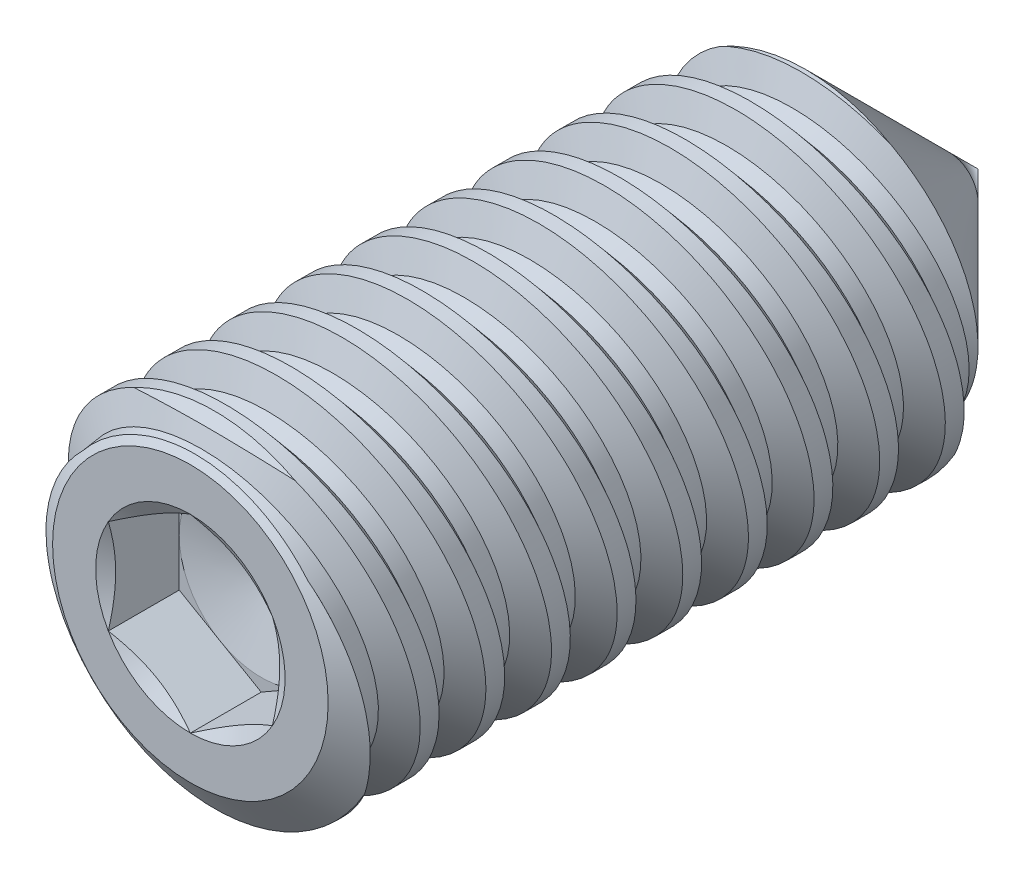
SolidWorks part; units mm, degrees
ref_plane "Front" through (0, 0, 0) normal (0, 0, 1) x (1, 0, 0)
ref_plane "Top" through (0, 0, 0) normal (0, 1, 0) x (1, 0, 0)
ref_plane "Right" through (0, 0, 0) normal (1, 0, 0) x (0, 0, -1)
sketch "Sketch22" plane through (0, 0, 0) normal (1, 0, 0) x (0, 0, -1)
  line L0 (-4.7625, 0) -> (-4.7625, 1.6662)
  line L1 (-4.7625, 1.6662) -> (-4.4708, 2.0828)
  line L2 (-4.4708, 2.0828) -> (2.6797, 2.0828)
  line L3 (2.6797, 2.0828) -> (4.7625, 2.0828) construction
  line L4 (2.6797, 2.0828) -> (4.7625, 0)
  line L5 (4.7625, 0) -> (-4.7625, 0)
  line L6 (5.271, 0) -> (4.7625, 0) construction
  line L7 (4.7625, 0) -> (4.7625, 2.0828) construction
  line L8 (2.6797, -2.0828) -> (4.7625, 0) construction
  line L10 (4.7625, -2.0828) -> (-4.7625, -2.0828) construction
  line L11 (-4.7625, -2.0828) -> (-4.7625, 0) construction
  line L12 (0, -2.0828) -> (0, 0) construction
  dimension "D1" = 7.4422
  dimension "Screw Dia" = 4.1656
  dimension "Length" = 9.525
  dimension "D3" = 35
  dimension "D7" = 3.3325
  dimension "Cone Point" = 90
revolve "Revolve1" add sketch "Sketch22" angle 360 about L6
sketch "Sketch6" plane through (0, 0, 0) normal (1, 0, 0) x (0, 0, -1)
  line L0 (1.9, 2.0828) -> (2.6937, -2.0828) construction
  line L1 (-4.4708, 2.0828) -> (2.6797, 2.0828) construction
  line L2 (2.6797, 2.0828) -> (2.6797, 2.2314) construction
  line L3 (1.9, 2.0828) -> (1.9974, 2.1014) construction
  line L4 (2.5165, 1.7629) -> (2.3215, 1.7258)
  line L5 (2.3215, 1.7258) -> (1.9974, 2.1014)
  line L6 (2.5165, 1.7629) -> (2.6797, 2.2314)
  line L7 (2.6797, 2.2314) -> (1.9974, 2.1014)
  line L8 (2.3545, 2.0828) -> (3.1482, -2.0828) construction
  line L9 (3.6028, 0.1622) -> (1.9, -0.1622) construction
  line L10 (2.3386, 2.1664) -> (2.419, 1.7443) construction
  line L12 (4.7625, -2.0828) -> (-4.7625, -2.0828) construction
  line L13 (1.9, -2.0828) -> (1.9, 2.0828) construction
  line L14 (1.9, -2.0828) -> (2.6937, -2.0828) construction
  line L15 (2.6937, -2.0828) -> (3.1482, -2.0828) construction
  line L18 (1.9, 2.0828) -> (2.3545, 2.0828) construction
  point P18 (2.7514, 0)
  dimension "D1" = 0.7937
  dimension "D2" = 0.1984
  dimension "D3" = 60
  dimension "D4" = 0.0992
  dimension "Pitch" = 0.7937
revolve "Cut-Revolve8" cut sketch "Sketch6" angle 360 about L9
pattern_linear "LPattern1" count 10 spacing 0.7937 along (0, 0, 1) count 2 spacing 0.7937 along (0, 0, 1) of "Cut-Revolve8"
sketch "Sketch23" plane through (0, 0, 4.7625) normal (0, 0, 1) x (1, 0, 0)
  line L1 (0, 1.1457) -> (-0.9922, 0.5728)
  line L2 (-0.9922, 0.5728) -> (-0.9922, -0.5728)
  line L3 (-0.9922, -0.5728) -> (0, -1.1457)
  line L4 (0, -1.1457) -> (0.9922, -0.5728)
  line L5 (0.9922, -0.5728) -> (0.9922, 0.5728)
  line L6 (0.9922, 0.5728) -> (0, 1.1457)
  circle A0 centre (0, 0) radius 0.9922 construction
  dimension "Hex" = 1.9844
extrude "Cut-Extrude10" cut sketch "Sketch23" against normal blind 0.8573
sketch "Sketch24" plane through (0, 0, 4.7625) normal (0, 0, 1) x (1, 0, 0)
  circle A0 centre (0, 0) radius 1.1457
extrude "Cut-Extrude11" cut sketch "Sketch24" against normal through all draft 60
sketch "Sketch26" plane through (0, 0, 3.9053) normal (0, 0, 1) x (1, 0, 0)
  circle A0 centre (0, 0) radius 0.9922 construction
  circle A1 centre (0, 0) radius 0.9922
extrude "Cut-Extrude12" cut sketch "Sketch26" against normal through all draft 75
sketch "Sketch27" plane through (0, 0, 0) normal (1, 0, 0) x (0, 0, -1)
  line L0 (4.7625, 0) -> (4.7805, 0.018) construction
  line L1 (4.7625, 0) -> (4.7805, -0.018) construction
  line L2 (5.271, 0) -> (4.7625, 0) construction
  line L3 (2.6797, 2.0828) -> (4.7625, 0) construction
  line L4 (2.6797, -2.0828) -> (4.7625, 0) construction
  dimension "D1" = 0.0254
equation "\"D2@Sketch6\"=\"Pitch@Sketch6\"/4"
equation "\"D4@Sketch6\"=\"Pitch@Sketch6\"/8"
equation "\"D1@Sketch6\"=\"Pitch@Sketch6\""
equation "\"D3@LPattern1\"=\"Pitch@Sketch6\""
equation "\"D1@LPattern1\"=(\"D1@Sketch22\"/\"Pitch@Sketch6\")+1"
equation "\"D4@LPattern1\"=\"Pitch@Sketch6\""
equation "\"D7@Sketch22\"=\"Screw Dia@Sketch22\"*.8"
